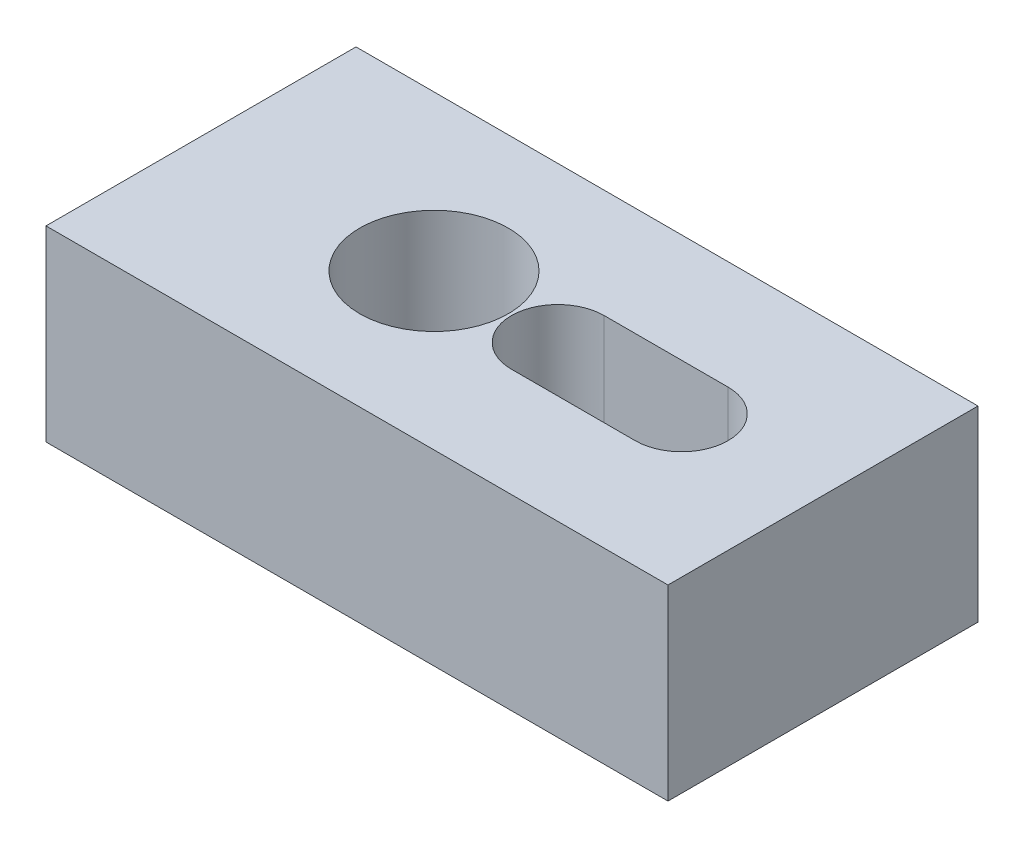
SolidWorks part; units mm, degrees
ref_plane "Front Plane" through (0, 0, 0) normal (0, 0, 1) x (1, 0, 0)
ref_plane "Top Plane" through (0, 0, 0) normal (0, 1, 0) x (1, 0, 0)
ref_plane "Right Plane" through (0, 0, 0) normal (1, 0, 0) x (0, 0, -1)
sketch "Sketch1" plane through (0, 0, 0) normal (0, 1, 0) x (1, 0, 0)
  line L0 (-40.3755, 45.955) -> (-27.6755, 45.955) construction
  line L1 (-76.9755, 61.855) -> (-13.1755, 61.855)
  line L2 (-76.9755, 61.855) -> (-76.9755, 30.055)
  line L3 (-76.9755, 30.055) -> (-13.1755, 30.055)
  line L4 (-13.1755, 61.855) -> (-13.1755, 30.055)
  line L5 (-40.3755, 50.7175) -> (-27.6755, 50.7175)
  line L6 (-40.3755, 41.1925) -> (-27.6755, 41.1925)
  circle A0 centre (-53.0755, 45.955) radius 7.62
  arc A1 (-40.3755, 50.7175) -> (-40.3755, 41.1925) centre (-40.3755, 45.955) ccw
  arc A2 (-27.6755, 41.1925) -> (-27.6755, 50.7175) centre (-27.6755, 45.955) ccw
  point P8 (-34.0255, 45.955)
  point P15 (-45.6859, 41.882)
  dimension "D5" = 15.24
  dimension "D6" = 4.7625
  dimension "D1" = 63.8
  dimension "D2" = 31.8
  dimension "D3" = 12.7
  dimension "D4" = 12.7
  dimension "D7" = 23.9
  dimension "D8" = 15.9
extrude "Boss-Extrude1" add sketch "Sketch1" along normal blind 19.2
